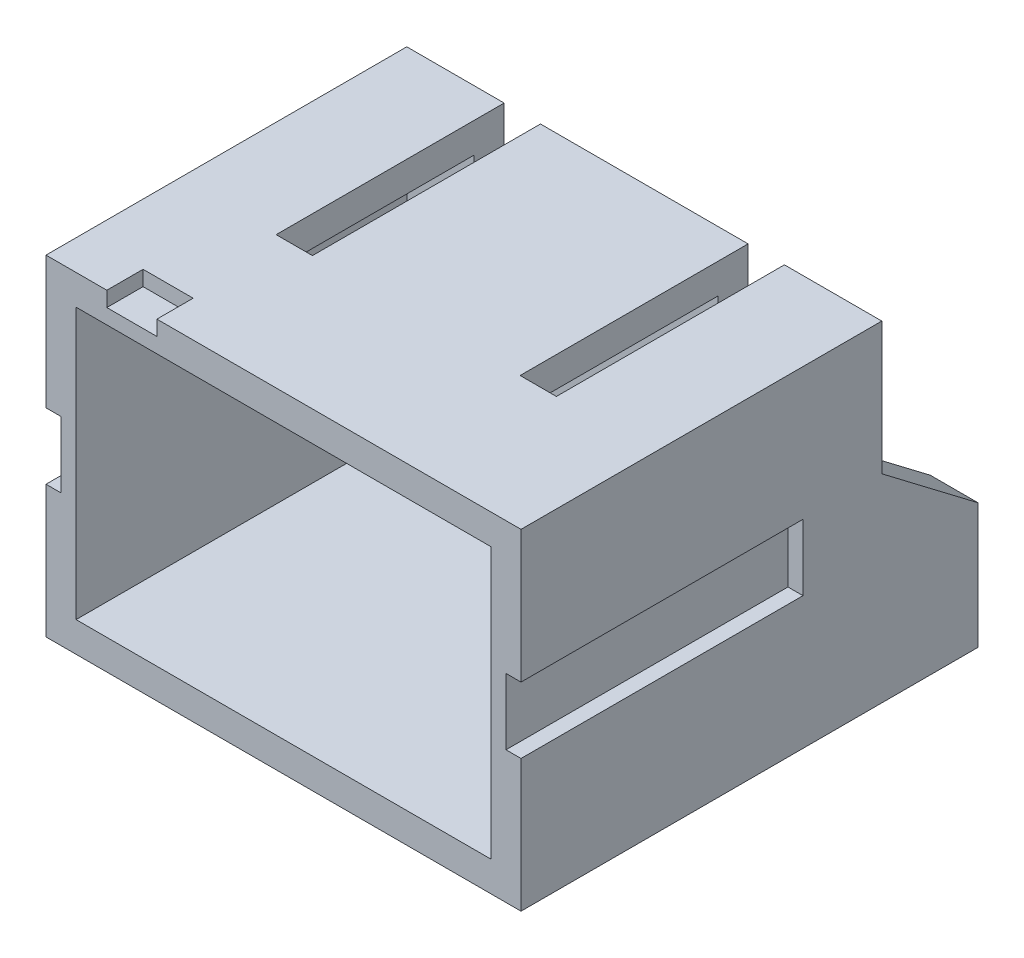
SolidWorks part; units mm, degrees
ref_plane "Front Plane" through (0, 0, 0) normal (0, 0, 1) x (1, 0, 0)
ref_plane "Top Plane" through (0, 0, 0) normal (0, 1, 0) x (1, 0, 0)
ref_plane "Right Plane" through (0, 0, 0) normal (1, 0, 0) x (0, 0, -1)
sketch "Sketch1" plane through (0, 0, 0) normal (1, 0, 0) x (0, 0, -1)
  line L0 (0, 0) -> (0, -3.3)
  line L2 (0, 0) -> (0, 2.2)
  line L3 (0, 2.2) -> (6, 2.2)
  line L4 (6, 0) -> (6, 2.2)
  line L5 (0, -3.3) -> (7.6, -3.3)
  line L6 (7.6, -3.3) -> (7.6, -1.2168)
  line L7 (6, 0) -> (7.6, -1.2168)
extrude "Boss-Extrude1" add sketch "Sketch1" along normal blind 7.9
sketch "Sketch4" plane through (0, 0, -7.6) normal (0, 0, -1) x (-1, 0, 0)
  line L0 (-7.9, -1.2168) -> (0, -1.2168) construction
  line L1 (-7.1078, 0.8664) -> (-0.7922, 0.8664)
  line L2 (-7.1078, 0.8664) -> (-7.1078, -3.3)
  line L3 (-7.1078, -3.3) -> (-0.7922, -3.3)
  line L4 (-0.7922, 0.8664) -> (-0.7922, -3.3)
  line L5 (-7.1078, 0.8664) -> (-0.7922, -3.3) construction
  line L6 (-7.1078, -3.3) -> (-0.7922, 0.8664) construction
  line L7 (-7.9, -3.3) -> (0, -3.3) construction
  point P0 (-3.95, -1.2168)
extrude "Cut-Extrude2" cut sketch "Sketch4" against normal up to surface (1.6 mm away) up to face at (3.95, 1.1, -6)
shell "Shell1" thickness 0.5
sketch "Sketch2" plane through (0, 2.2, 0) normal (0, 1, 0) x (1, 0, 0)
  line L0 (3.95, 6) -> (3.95, 0) construction
  line L1 (7.9, 6) -> (0, 6) construction
  line L2 (7.9, 0) -> (0, 0) construction
  line L3 (2.2233, 9.792) -> (1.6195, 2.208) construction
  line L4 (5.6767, 2.208) -> (6.2805, 2.208)
  line L5 (5.6767, 2.208) -> (5.6767, 9.792)
  line L6 (5.6767, 9.792) -> (6.2805, 9.792)
  line L7 (6.2805, 2.208) -> (6.2805, 9.792)
  line L8 (5.6767, 2.208) -> (6.2805, 9.792) construction
  line L9 (5.6767, 9.792) -> (6.2805, 2.208) construction
  line L10 (2.2233, 2.208) -> (1.6195, 9.792) construction
  line L11 (1.6195, 2.208) -> (1.6195, 9.792)
  line L12 (2.2233, 9.792) -> (1.6195, 9.792)
  line L13 (2.2233, 2.208) -> (2.2233, 9.792)
  line L14 (2.2233, 2.208) -> (1.6195, 2.208)
  point P6 (5.9786, 6)
  point P15 (1.9214, 6)
extrude "Cut-Extrude1" cut sketch "Sketch2" against normal blind 1.55
sketch "Sketch5" plane through (0, 2.2, 0) normal (0, 1, 0) x (1, 0, 0)
  line L0 (7.9, 0) -> (0, 0) construction
  line L1 (1.0117, -0.6025) -> (1.8445, -0.6025)
  line L2 (1.0117, -0.6025) -> (1.0117, 0.6025)
  line L3 (1.0117, 0.6025) -> (1.8445, 0.6025)
  line L4 (1.8445, -0.6025) -> (1.8445, 0.6025)
  line L5 (1.0117, -0.6025) -> (1.8445, 0.6025) construction
  line L6 (1.0117, 0.6025) -> (1.8445, -0.6025) construction
  point P0 (1.4281, 0)
extrude "Cut-Extrude3" cut sketch "Sketch5" against normal blind 0.25
ref_plane "Plane1" through (3.95, 0, 0) normal (-1, 0, 0) x (0, 0, 1)
sketch "Sketch6" plane through (0, 0, 0) normal (-1, 0, 0) x (0, 0, 1)
  line L0 (0, 2.2) -> (0, -3.3) construction
  line L1 (-4.6894, -1.1) -> (4.6894, -1.1)
  line L2 (-4.6894, -1.1) -> (-4.6894, 0)
  line L3 (-4.6894, 0) -> (4.6894, 0)
  line L4 (4.6894, -1.1) -> (4.6894, 0)
  line L5 (-4.6894, -1.1) -> (4.6894, 0) construction
  line L6 (-4.6894, 0) -> (4.6894, -1.1) construction
  point P0 (0, -0.55)
extrude "Cut-Extrude4" cut sketch "Sketch6" against normal blind 0.25
mirror "Mirror1" about plane through (3.95, 0, 0) normal (-1, 0, 0) of "Cut-Extrude4"
